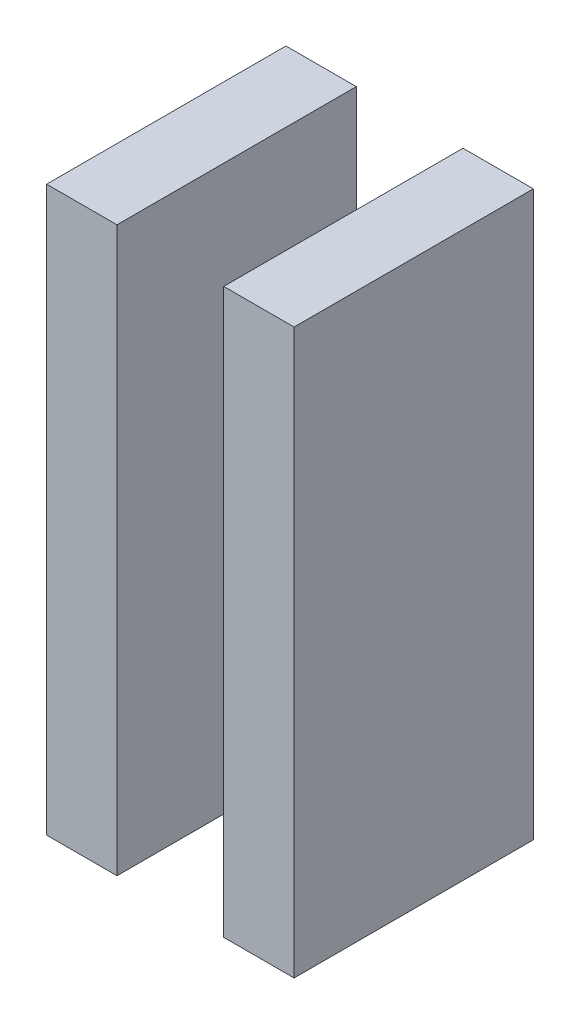
SolidWorks part; units mm, degrees
ref_plane "Ebene vorne" through (0, 0, 0) normal (0, 0, 1) x (1, 0, 0)
ref_plane "Ebene oben" through (0, 0, 0) normal (0, 1, 0) x (1, 0, 0)
ref_plane "Ebene rechts" through (0, 0, 0) normal (1, 0, 0) x (0, 0, -1)
sketch "Skizze1" plane through (0, 0, 0) normal (0, 0, 1) x (1, 0, 0)
  line L0 (150.3175, -54.445) -> (148.2875, -54.445) construction
  line L1 (147.8325, -54.445) -> (150.7725, -54.445)
  line L2 (147.8325, -54.445) -> (147.8325, -78.005)
  line L3 (147.8325, -78.005) -> (150.7725, -78.005)
  line L4 (150.7725, -54.445) -> (150.7725, -78.005)
  line L9 (148.285, -78.005) -> (150.315, -78.005) construction
  line L10 (153.0025, -67.1355) -> (153.0025, -72.5563) construction
  line L11 (155.2325, -54.445) -> (155.2325, -78.005)
  line L12 (158.1725, -78.005) -> (155.2325, -78.005)
  line L13 (158.1725, -54.445) -> (158.1725, -78.005)
  line L14 (158.1725, -54.445) -> (155.2325, -54.445)
  arc A0 (150.3175, -60.055) -> (150.3175, -59.145) centre (150.3175, -59.6) ccw construction
  arc A1 (148.2875, -59.145) -> (148.2875, -60.055) centre (148.2875, -59.6) ccw construction
  arc A2 (155.6875, -54.4425) -> (155.6875, -55.3525) centre (155.6875, -54.8975) ccw construction
  point P23 (155.2325, -54.8975)
extrude "Aufsatz-Linear austragen1" add sketch "Skizze1" along normal blind 10 from offset 1
